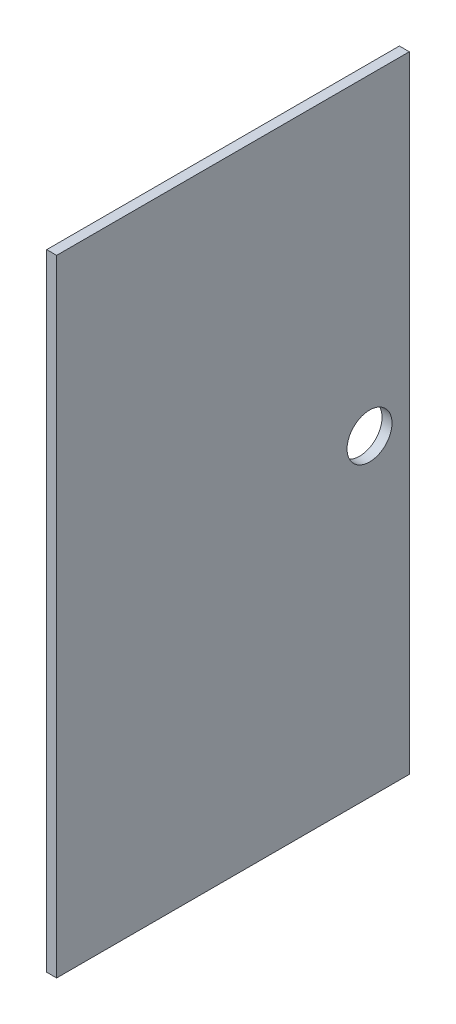
SolidWorks part; units mm, degrees
ref_plane "Front Plane" through (0, 0, 0) normal (0, 0, 1) x (1, 0, 0)
ref_plane "Top Plane" through (0, 0, 0) normal (0, 1, 0) x (1, 0, 0)
ref_plane "Right Plane" through (0, 0, 0) normal (1, 0, 0) x (0, 0, -1)
sketch "Sketch1" plane through (0, 0, 0) normal (1, 0, 0) x (0, 0, -1)
  line L1 (0, 0) -> (225.298, 0)
  line L2 (0, 0) -> (0, 399.796)
  line L3 (0, 399.796) -> (225.298, 399.796)
  line L4 (225.298, 0) -> (225.298, 399.796)
  dimension "D1" = 225.298
  dimension "D2" = 399.796
extrude "Boss-Extrude1" add sketch "Sketch1" along normal blind 6.35
sketch "Sketch2" plane through (6.35, 0, 0) normal (1, 0, 0) x (0, 0, -1)
  line L0 (0, 0) -> (225.298, 0) construction
  line L1 (225.298, 0) -> (225.298, 399.796) construction
  circle A0 centre (199.898, 199.898) radius 14.351
  dimension "D1" = 28.702
  dimension "D2" = 199.898
  dimension "D3" = 25.4
extrude "Cut-Extrude1" cut sketch "Sketch2" against normal through all both and the other way through all
